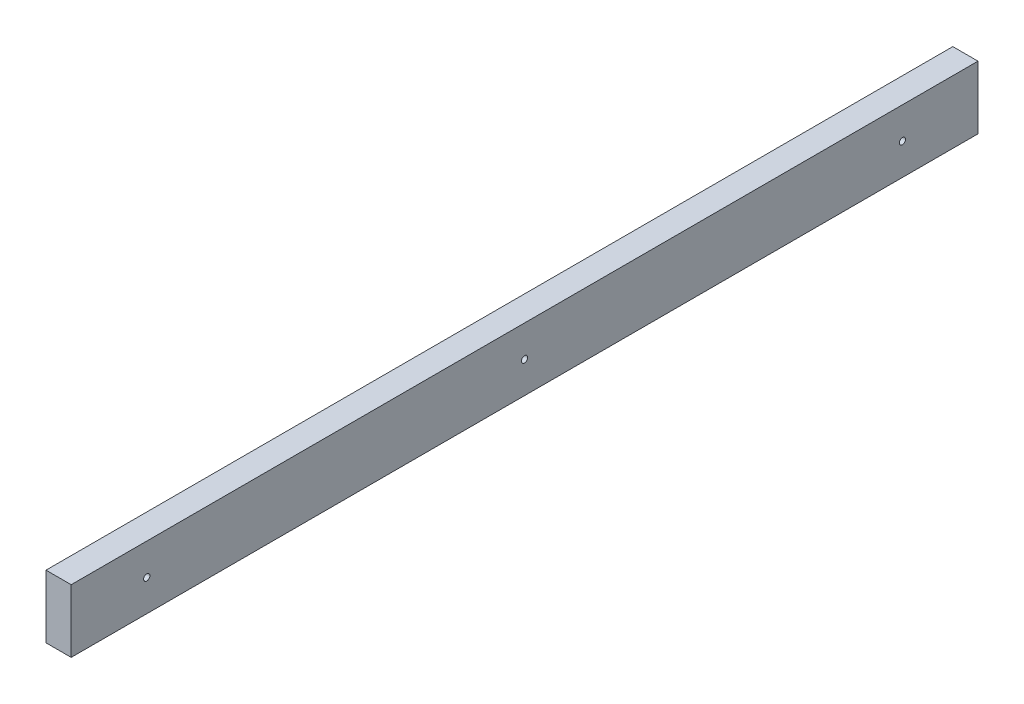
SolidWorks part; units mm, degrees
material "Cedar"
ref_plane "Front" through (0, 0, 0) normal (0, 0, 1) x (1, 0, 0)
ref_plane "Top" through (0, 0, 0) normal (0, 1, 0) x (1, 0, 0)
ref_plane "Right" through (0, 0, 0) normal (1, 0, 0) x (0, 0, -1)
sketch "Sketch1" plane through (0, 0, 0) normal (0, 0, 1) x (1, 0, 0)
  line L0 (0, 0) -> (0, -31.75)
  line L1 (0, -31.75) -> (12.7, -31.75)
  line L2 (12.7, -31.75) -> (12.7, 0)
  line L3 (12.7, 0) -> (0, 0)
extrude "Extrude1" add sketch "Sketch1" along normal mid plane 457.2
sketch "Sketch2" plane through (12.7, 0, 0) normal (1, 0, 0) x (0, 0, -1)
  line L0 (-228.6, -15.875) -> (-190.5, -15.875) construction
  line L1 (-228.6, -31.75) -> (-228.6, 0) construction
  line L2 (228.6, -15.875) -> (190.5, -15.875) construction
  line L3 (228.6, -31.75) -> (228.6, 0) construction
  line L4 (-190.5, -15.875) -> (190.5, -15.875) construction
  circle A0 centre (-190.5, -15.875) radius 1.5875
  circle A1 centre (190.5, -15.875) radius 1.5875
  circle A2 centre (0, -15.875) radius 1.5875
extrude "Cut-Extrude1" cut sketch "Sketch2" against normal up to surface (12.7 mm away) up to face at (0, -15.875, 0)
